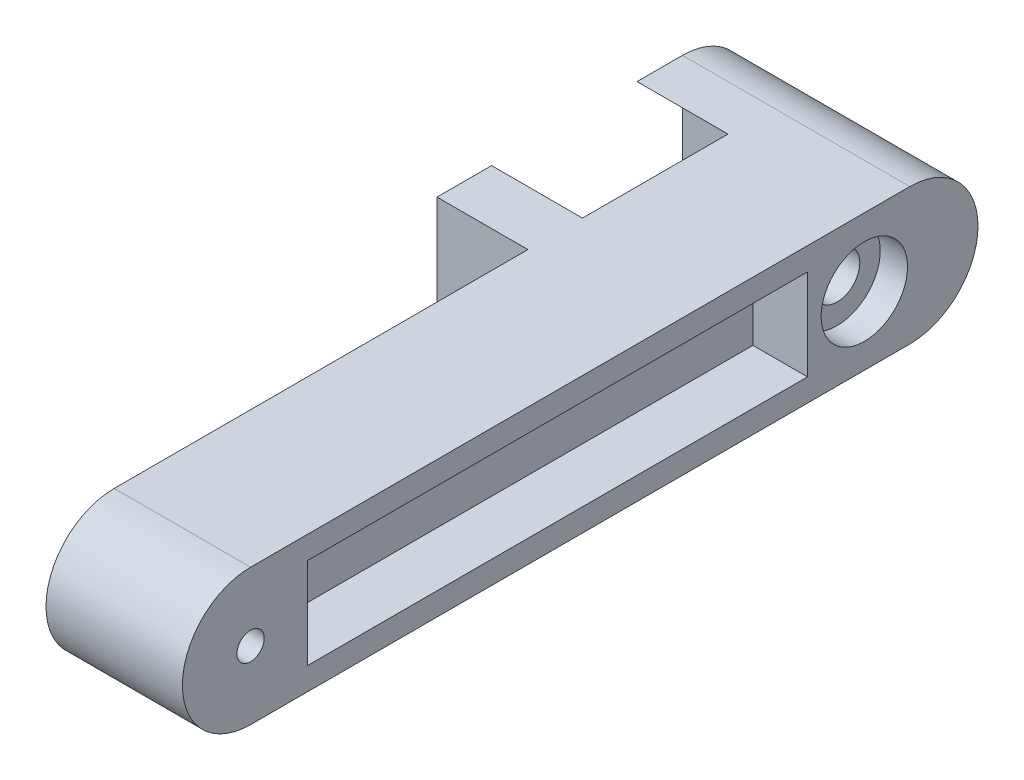
SolidWorks part; units mm, degrees
ref_plane "Front Plane" through (0, 0, 0) normal (0, 0, 1) x (1, 0, 0)
ref_plane "Top Plane" through (0, 0, 0) normal (0, 1, 0) x (1, 0, 0)
ref_plane "Right Plane" through (0, 0, 0) normal (1, 0, 0) x (0, 0, -1)
sketch "Sketch1" plane through (0, 0, 0) normal (1, 0, 0) x (0, 0, -1)
  line L0 (0, 30) -> (135, 30)
  line L1 (135, 0) -> (0, 0)
  arc A0 (135, 30) -> (135, 0) centre (135, 15) cw
  arc A1 (0, 0) -> (0, 30) centre (0, 15) cw
  dimension "D1" = 135
  dimension "D2" = 30
extrude "Boss-Extrude1" add sketch "Sketch1" along normal blind 30
sketch "Sketch2" plane through (30, 0, 0) normal (1, 0, 0) x (0, 0, -1)
  circle A0 centre (0, 15) radius 3
  dimension "D1" = 6
extrude "Cut-Extrude1" cut sketch "Sketch2" against normal blind 30
sketch "Sketch3" plane through (30, 0, 0) normal (1, 0, 0) x (0, 0, -1)
  circle A0 centre (135, 15) radius 9.5
  dimension "D1" = 19
extrude "Cut-Extrude2" cut sketch "Sketch3" against normal blind 6
sketch "Sketch4" plane through (0, 0, 0) normal (-1, 0, 0) x (0, 0, 1)
  circle A0 centre (-135, 15) radius 9.5
  dimension "D1" = 19
extrude "Cut-Extrude3" cut sketch "Sketch4" against normal blind 6
sketch "Sketch5" plane through (6, 0, 0) normal (-1, 0, 0) x (0, 0, 1)
  circle A0 centre (-135, 15) radius 5
  dimension "D1" = 10
extrude "Cut-Extrude4" cut sketch "Sketch5" against normal up to next
scale "Scale1" [suppressed]
sketch "Sketch6" plane through (30, 0, 0) normal (1, 0, 0) x (0, 0, -1)
  line L1 (12.5, 25) -> (122.5, 25)
  line L2 (12.5, 25) -> (12.5, 5)
  line L3 (12.5, 5) -> (122.5, 5)
  line L4 (122.5, 25) -> (122.5, 5)
  line L5 (12.5, 25) -> (122.5, 5) construction
  line L6 (12.5, 5) -> (122.5, 25) construction
  point P0 (67.5, 15)
  dimension "D1" = 20
  dimension "D2" = 110
extrude "Cut-Extrude5" cut sketch "Sketch6" against normal blind 12
sketch "Sketch7" plane through (0, 0, 0) normal (-1, 0, 0) x (0, 0, 1)
  line L1 (-12.5, 5) -> (-122.5, 5)
  line L2 (-12.5, 5) -> (-12.5, 25)
  line L3 (-12.5, 25) -> (-122.5, 25)
  line L4 (-122.5, 5) -> (-122.5, 25)
  line L5 (-12.5, 5) -> (-122.5, 25) construction
  line L6 (-12.5, 25) -> (-122.5, 5) construction
  point P0 (-67.5, 15)
  dimension "D1" = 20
  dimension "D2" = 110
extrude "Cut-Extrude6" cut sketch "Sketch7" against normal blind 12
sketch "Sketch8" plane through (12, 0, 0) normal (-1, 0, 0) x (0, 0, 1)
  line L0 (-135, 30) -> (0, 30) construction
  line L1 (-103, 30) -> (-91, 30)
  line L2 (-103, 30) -> (-103, 0)
  line L3 (-103, 0) -> (-91, 0)
  line L4 (-91, 30) -> (-91, 0)
  line L5 (0, 0) -> (-135, 0) construction
  line L6 (-135, 15) -> (-135, 51.1309) construction
  line L7 (-145, 0) -> (-157, 0)
  line L8 (-145, 0) -> (-145, 30)
  line L9 (-145, 30) -> (-157, 30)
  line L10 (-157, 0) -> (-157, 30)
  line L11 (-91, 30) -> (-175.1648, 30) construction
  line L12 (-91, 0) -> (-167.1663, 0) construction
  dimension "D1" = 32
  dimension "D2" = 10
  dimension "D3" = 12
  dimension "D4" = 12
extrude "Boss-Extrude2" add sketch "Sketch8" along normal blind 32
sketch "Sketch9" plane through (12, 0, 0) normal (1, 0, 0) x (0, 0, -1)
  line L5 (145, 30) -> (145, 26.1803)
  line L6 (145, 3.8197) -> (145, 0)
  line L7 (145, 0) -> (157, 0)
  line L8 (157, 0) -> (157, 30)
  line L9 (157, 30) -> (145, 30)
  line L10 (145, 30) -> (145, 26.1803)
  line L11 (145, 3.8197) -> (145, 0)
  line L12 (145, 0) -> (157, 0)
  line L13 (157, 0) -> (157, 30)
  line L14 (157, 30) -> (145, 30)
  arc A1 (145, 3.8197) -> (145, 26.1803) centre (135, 15) ccw
  arc A2 (145, 3.8197) -> (145, 26.1803) centre (135, 15) ccw
  dimension "D1" = 0
extrude "Cut-Extrude7" cut sketch "Sketch9" against normal blind 35
sketch "Sketch10" plane through (30, 0, 0) normal (1, 0, 0) x (0, 0, -1)
  line L0 (135, 30) -> (145, 30)
  line L1 (145, 0) -> (135, 0)
  arc A0 (135, 0) -> (135, 30) centre (135, 15) ccw construction
  arc A1 (145, 30) -> (145, 0) centre (145, 15) cw
  arc A2 (135, 0) -> (135, 30) centre (135, 15) ccw
  dimension "D1" = 10
extrude "Boss-Extrude3" add sketch "Sketch10" against normal up to surface (50 mm away) up to face at (-20, 15, -147.5)
sketch "Sketch11" plane through (-20, 0, 0) normal (-1, 0, 0) x (0, 0, 1)
  circle A0 centre (-149.85, 10.3502) radius 1.5
  dimension "D1" = 3
sketch "Sketch12" plane through (-20, 0, 0) normal (-1, 0, 0) x (0, 0, 1)
  circle A0 centre (-99.35, 10.3502) radius 1.5
  dimension "D1" = 3
sketch "Sketch13" plane through (-20, 0, 0) normal (-1, 0, 0) x (0, 0, 1)
  circle A0 centre (-149.85, 20.3502) radius 1.5
  circle A1 centre (-99.35, 20.3502) radius 1.5
  dimension "D1" = 3
  dimension "D2" = 3
extrude "Cut-Extrude8" cut sketch "Sketch11" against normal blind 10
extrude "Cut-Extrude9" cut sketch "Sketch13" against normal blind 10
extrude "Cut-Extrude10" cut sketch "Sketch12" against normal blind 10
